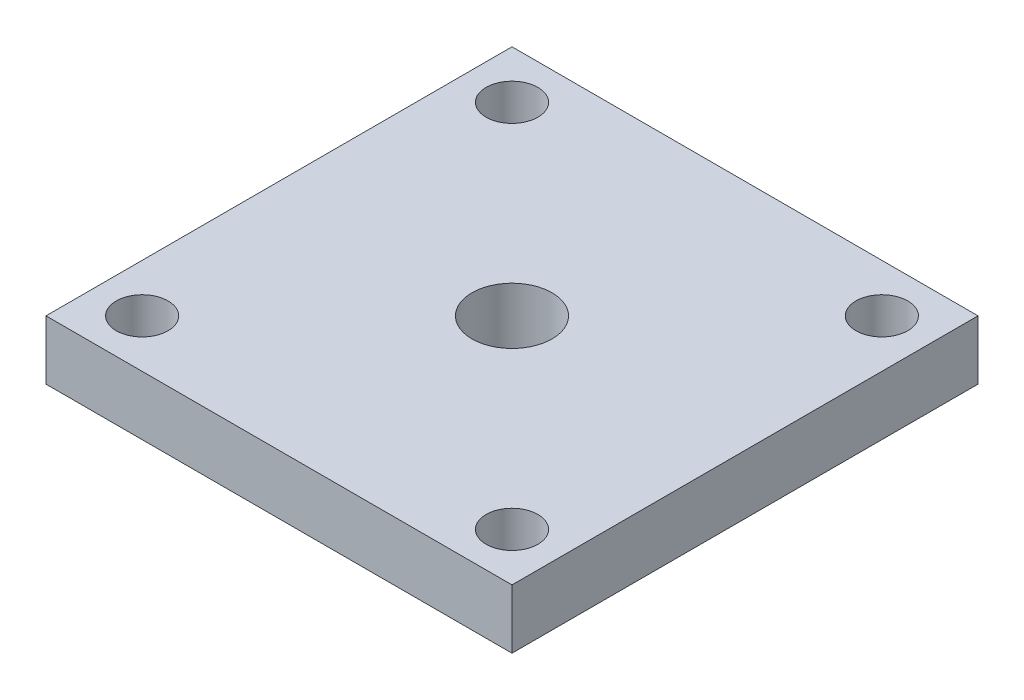
SolidWorks part; units mm, degrees
ref_plane "Front Plane" through (0, 0, 0) normal (0, 0, 1) x (1, 0, 0)
ref_plane "Top Plane" through (0, 0, 0) normal (0, 1, 0) x (1, 0, 0)
ref_plane "Right Plane" through (0, 0, 0) normal (1, 0, 0) x (0, 0, -1)
sketch "Sketch1" plane through (0, 0, 0) normal (0, 1, 0) x (1, 0, 0)
  line L1 (-15.75, -15.75) -> (15.75, -15.75)
  line L2 (-15.75, -15.75) -> (-15.75, 15.75)
  line L3 (-15.75, 15.75) -> (15.75, 15.75)
  line L4 (15.75, -15.75) -> (15.75, 15.75)
  line L5 (-15.75, -15.75) -> (15.75, 15.75) construction
  line L6 (-15.75, 15.75) -> (15.75, -15.75) construction
  point P0 (0, 0)
  dimension "D1" = 31.5
  dimension "D2" = 31.5
extrude "Boss-Extrude1" add sketch "Sketch1" along normal blind 4
hole_wizard "Ø3.5 (3.5) Diameter Hole1" positions "Sketch2" profile "Sketch3" hole size "Ø3.5" standard "ANSI Metric" end condition through all
sketch "Sketch2" plane through (0, 4, 0) normal (0, 1, 0) x (1, 0, 0)
  line L0 (-15.75, 15.75) -> (-15.75, -15.75) construction
  line L1 (15.75, 15.75) -> (-15.75, 15.75) construction
  point P0 (-12.5, 12.5)
  point P2 (12.5, 12.5)
  point P4 (12.5, -12.5)
  point P6 (-12.5, -12.5)
  dimension "D1" = 25
  dimension "D2" = 25
  dimension "D3" = 3.25
  dimension "D4" = 3.25
sketch "Sketch3" plane through (-12.5, 4, -12.5) normal (1, 0, 0) x (0, 0, 1)
  line L0 (0, 0) -> (0, 4)
  line L1 (0, 4) -> (1.75, 4)
  line L2 (1.75, 4) -> (1.75, 0)
  line L5 (1.75, 0) -> (0, 0)
  line L11 (0, -6.35) -> (0, 107.95) construction
  dimension "Thru Hole Dia." = 3.5
  dimension "Thru Hole Depth" = 4
hole_wizard "1/4-28 Tapped Hole1" positions "Sketch4" profile "Sketch5" tap size "1/4-28" standard "ANSI Inch" end condition through all
sketch "Sketch4" plane through (0, 4, 0) normal (0, 1, 0) x (1, 0, 0)
  point P0 (0, 0)
sketch "Sketch5" plane through (0, 4, 0) normal (1, 0, 0) x (0, 0, 1)
  line L0 (0, 0) -> (0, 4)
  line L1 (0, 4) -> (2.7051, 4)
  line L2 (2.7051, 4) -> (2.7051, 0)
  line L5 (2.7051, 0) -> (0, 0)
  line L11 (0, -6.35) -> (0, 107.95) construction
  dimension "Thru Tap Drill Dia." = 5.4102
  dimension "Thru Tap Drill Depth" = 4
cosmetic thread "Hole Thread1" parameters "D2"=6.35
